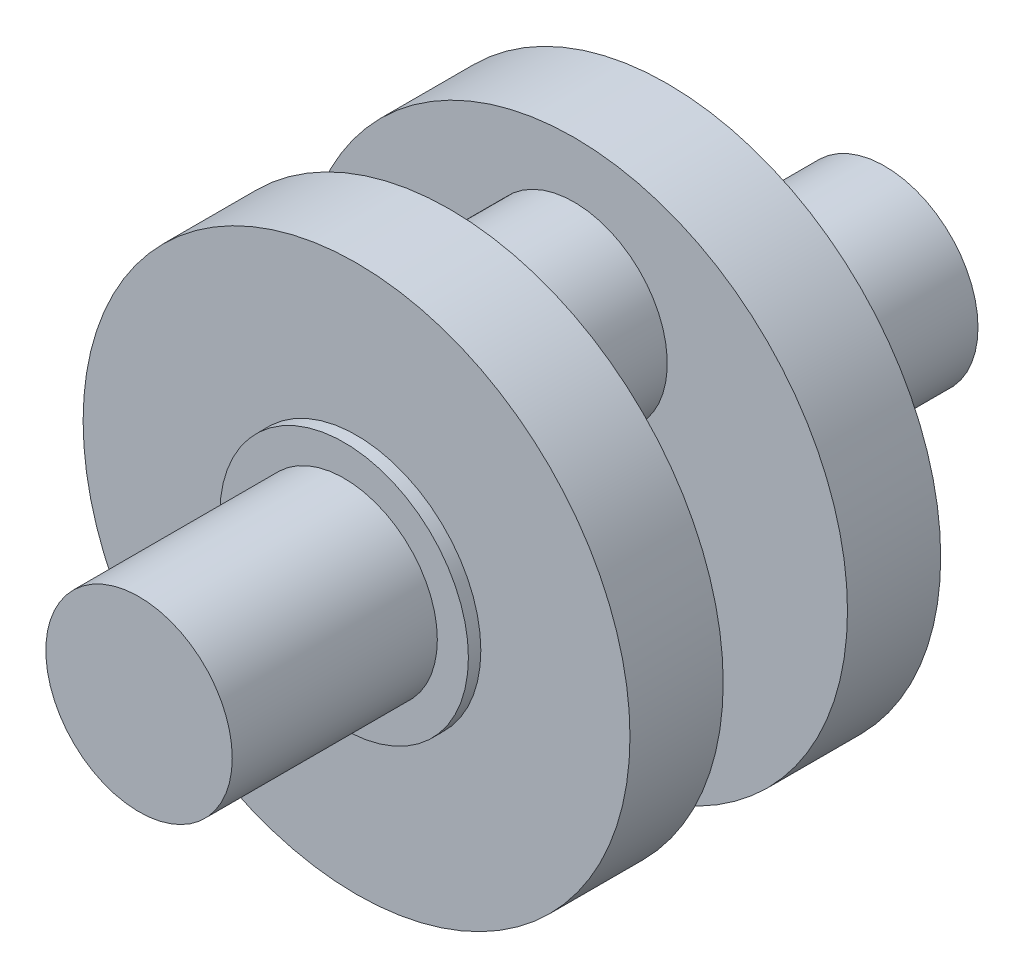
SolidWorks part; units mm, degrees
ref_plane "Front Plane" through (0, 0, 0) normal (0, 0, 1) x (1, 0, 0)
ref_plane "Top Plane" through (0, 0, 0) normal (0, 1, 0) x (1, 0, 0)
ref_plane "Right Plane" through (0, 0, 0) normal (1, 0, 0) x (0, 0, -1)
sketch "Szkic1" plane through (0, 0, 0) normal (0, 0, 1) x (1, 0, 0)
  circle A0 centre (0, 0) radius 15
  dimension "D1" = 30
extrude "Dodanie-wyciągnięcie1" add sketch "Szkic1" along normal blind 33
sketch "Szkic2" plane through (0, 0, 0) normal (0, 0, -1) x (-1, 0, 0)
  circle A0 centre (0, 0) radius 20
  dimension "D1" = 40
extrude "Dodanie-wyciągnięcie2" add sketch "Szkic2" along normal blind 2 contours A0
sketch "Szkic3" plane through (0, 0, -2) normal (0, 0, -1) x (-1, 0, 0)
  circle A0 centre (0, 0) radius 44
  dimension "D1" = 88
extrude "Dodanie-wyciągnięcie3" add sketch "Szkic3" along normal blind 15
sketch "Szkic4" plane through (0, 0, -17) normal (0, 0, -1) x (-1, 0, 0)
  circle A0 centre (0, 20) radius 15
  point P2 (0, 0)
  dimension "D1" = 30
  dimension "D2" = 20
extrude "Dodanie-wyciągnięcie4" add sketch "Szkic4" along normal blind 10 contours A0
mirror "Lustro1" about plane through (0, 20, -27) normal (0, 0, -1) of bodies 104
